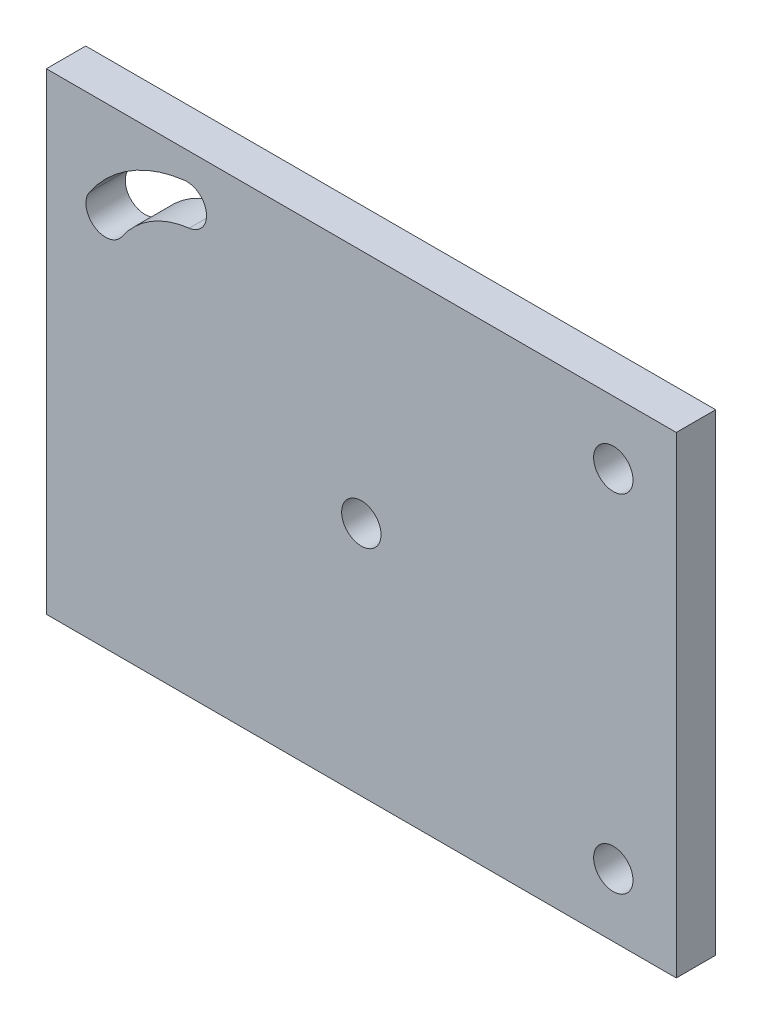
SolidWorks part; units mm, degrees
ref_plane "Front Plane" through (0, 0, 0) normal (0, 0, 1) x (1, 0, 0)
ref_plane "Top Plane" through (0, 0, 0) normal (0, 1, 0) x (1, 0, 0)
ref_plane "Right Plane" through (0, 0, 0) normal (1, 0, 0) x (0, 0, -1)
sketch "Sketch1" plane through (0, 0, 0) normal (0, 0, 1) x (1, 0, 0)
  line L1 (0, 0) -> (80, 0)
  line L2 (0, 0) -> (0, -60)
  line L3 (0, -60) -> (80, -60)
  line L4 (80, 0) -> (80, -60)
  circle A0 centre (40, -30) radius 2.5
  point P4 (0, 0)
  point P8 (40, 0)
  dimension "D4" = 5
  dimension "D1" = 80
  dimension "D2" = 60
  dimension "D3" = 30
extrude "Boss-Extrude1" add sketch "Sketch1" along normal blind 5
sketch "Sketch2" plane through (0, 0, 5) normal (0, 0, 1) x (1, 0, 0)
  line L0 (0, -60) -> (80, -60) construction
  line L1 (80, -60) -> (80, 0) construction
  line L2 (80, 0) -> (0, 0) construction
  line L3 (0, 0) -> (0, -60) construction
  circle A0 centre (72, -52) radius 2.5
  circle A1 centre (72, -8) radius 2.5
  arc A2 (7.5265, -12.2694) -> (17.8456, -5.9828) centre (19.544, -20.383) cw construction
  arc A3 (17.5528, -3.5) -> (5.4545, -10.8706) centre (19.544, -20.383) ccw
  arc A4 (18.1385, -8.4656) -> (9.5985, -13.6683) centre (19.544, -20.383) ccw
  arc A5 (18.1385, -8.4656) -> (17.5528, -3.5) centre (17.8456, -5.9828) ccw
  arc A6 (5.4545, -10.8706) -> (9.5985, -13.6683) centre (7.5265, -12.2694) ccw
  point P13 (12, -8)
  dimension "D1" = 5
  dimension "D2" = 5
  dimension "D4" = 8
  dimension "D5" = 8
  dimension "D6" = 8
  dimension "D7" = 2.5
  dimension "D10" = 12
  dimension "D3" = 8
  dimension "D8" = 8
  dimension "D9" = 12
  dimension "D11" = 10
  dimension "D12" = 3.5
extrude "Cut-Extrude1" cut sketch "Sketch2" against normal through all
